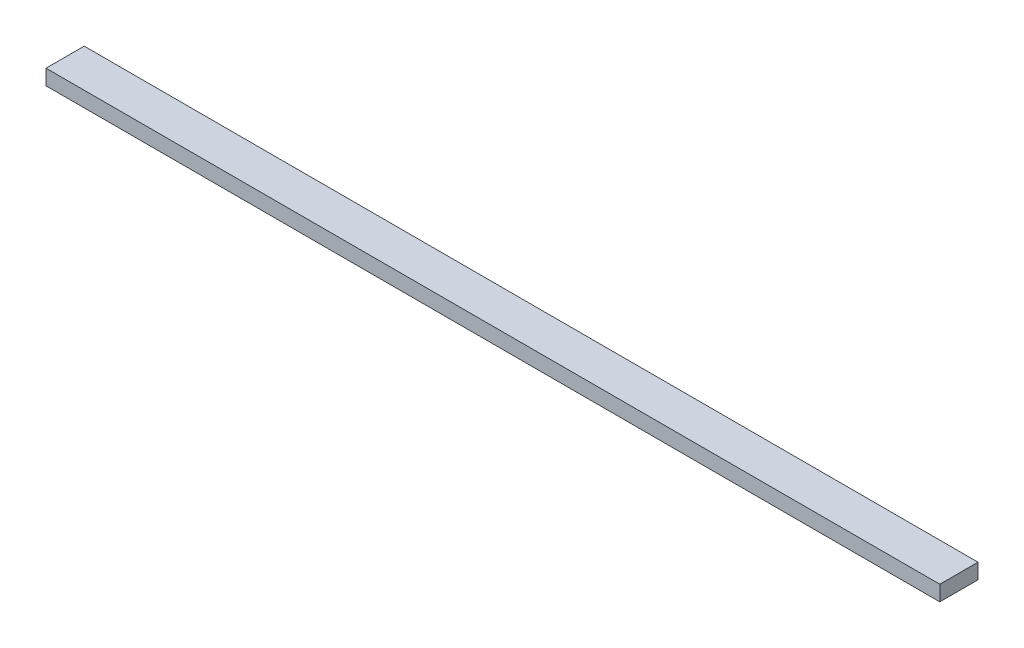
SolidWorks part; units mm, degrees
material "AISI 304"
ref_plane "Front Plane" through (0, 0, 0) normal (0, 0, 1) x (1, 0, 0)
ref_plane "Top Plane" through (0, 0, 0) normal (0, 1, 0) x (1, 0, 0)
ref_plane "Right Plane" through (0, 0, 0) normal (1, 0, 0) x (0, 0, -1)
sketch "Sketch1" plane through (0, 0, 0) normal (1, 0, 0) x (0, 0, -1)
  line L1 (0, 0) -> (63.5, 0)
  line L2 (0, 0) -> (0, 25.4)
  line L3 (0, 25.4) -> (63.5, 25.4)
  line L4 (63.5, 0) -> (63.5, 25.4)
  dimension "D1" = 63.5
  dimension "D2" = 25.4
extrude "Boss-Extrude1" add sketch "Sketch1" along normal blind 1486.154
